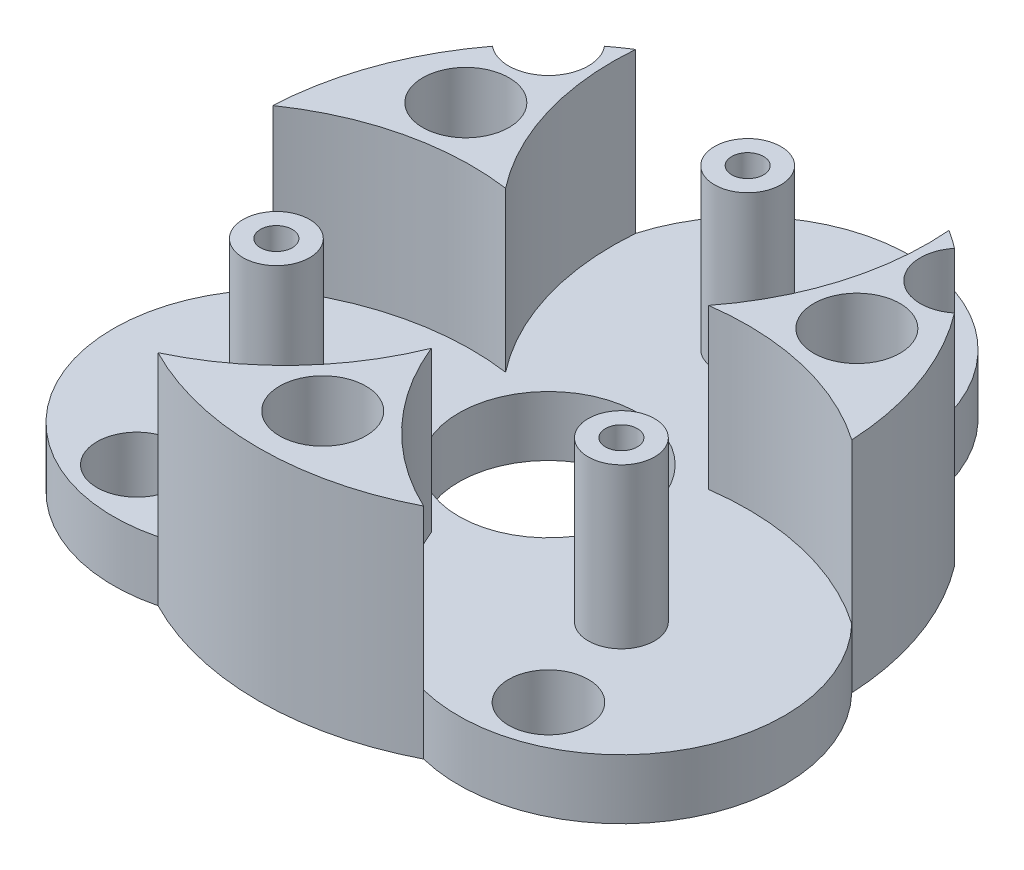
SolidWorks part; units mm, degrees
ref_plane "Alzado" through (0, 0, 0) normal (0, 0, 1) x (1, 0, 0)
ref_plane "Planta" through (0, 0, 0) normal (0, 1, 0) x (1, 0, 0)
ref_plane "Vista lateral" through (0, 0, 0) normal (1, 0, 0) x (0, 0, -1)
sketch "Croquis1" plane through (0, 0, 0) normal (0, 1, 0) x (1, 0, 0)
  circle A0 centre (0, 0) radius 5 construction
  circle A1 centre (0, 15) radius 10 construction
  circle A2 centre (0, 0) radius 25 construction
  circle A7 centre (0, 0) radius 21.825
  point P24 (0, 0)
  dimension "D1" = 10
  dimension "D2" = 20
  dimension "D3" = 43.65
extrude "Saliente-Extruir1" add sketch "Croquis1" along normal blind 4.5
sketch "Croquis2" plane through (0, 4.5, 0) normal (0, 1, 0) x (1, 0, 0)
  circle A0 centre (0, 0) radius 15 construction
  circle A1 centre (0, 15) radius 2.5
  circle A2 centre (12.9904, -7.5) radius 2.5
  circle A3 centre (-12.9904, -7.5) radius 2.5
  point P12 (0, 0)
  dimension "D1" = 30
  dimension "D2" = 5
  dimension "D3" = 3
extrude "Saliente-Extruir2" add sketch "Croquis2" along normal blind 12
hole_wizard "Taladro de margen para M121" positions "Croquis3" profile "Croquis4" hole size "M12" standard "ISO" end condition through all
sketch "Croquis3" plane through (0, 4.5, 0) normal (0, 1, 0) x (1, 0, 0)
  point P0 (0, 0)
sketch "Croquis4" plane through (0, 4.5, 0) normal (1, 0, 0) x (0, 0, 1)
  line L0 (0, 0) -> (0, 4.5)
  line L1 (0, 4.5) -> (6.75, 4.5)
  line L2 (6.75, 4.5) -> (6.75, 0)
  line L5 (6.75, 0) -> (0, 0)
  line L11 (0, -6.35) -> (0, 107.95) construction
  dimension "Diámetro de taladro hasta el siguiente" = 13.5
  dimension "Profundidad de taladro hasta el siguiente" = 4.5
sketch "Croquis5" plane through (0, 4.5, 0) normal (0, 1, 0) x (1, 0, 0)
  line L0 (0, 0) -> (-18.901, 10.9125) construction
  line L1 (-12.9904, -7.5) -> (0, 15) construction
  circle A0 centre (-12.9904, -7.5) radius 8.25 construction
  circle A1 centre (0, 15) radius 8.25 construction
  arc A4 (-7.6427, 4.4125) -> (-11.8002, 18.3599) centre (8.1271, 16.7067) cw
  arc A5 (-7.6427, 4.4125) -> (-21.8002, 1.0394) centre (-10.4048, -15.3916) ccw
  arc A6 (-11.8002, 18.3599) -> (-21.8002, 1.0394) centre (0, 0) ccw
  circle A7 centre (0, 0) radius 21.825 construction
  dimension "D1" = 20
  dimension "D2" = 13
extrude "Saliente-Extruir3" add sketch "Croquis5" along normal up to surface (12 mm away) up to face at (-12.9904, 16.5, 10)
sketch "Croquis8" plane through (0, 16.5, 0) normal (0, 1, 0) x (1, 0, 0)
  line L0 (-7.6427, 4.4125) -> (-18.901, 10.9125) construction
  circle A1 centre (-14.7224, 8.5) radius 1.7
  circle A2 centre (0, 0) radius 15 construction
  arc A3 (-11.8002, 18.3599) -> (-21.8002, 1.0394) centre (0, 0) ccw construction
  circle A4 centre (0, 0) radius 17 construction
  dimension "D1" = 3.4
  dimension "D2" = 2
extrude "Cortar-Extruir1" cut sketch "Croquis8" against normal up to surface (16.5 mm away) up to face at (0, 0, 6.75)
pattern_circular "MatrizC1" count 3 every 120 about axis through (0, 0, 0) along (0, 1, 0) of "Saliente-Extruir3", "Cortar-Extruir1"
hole_wizard "Taladro de margen para M21" positions "Croquis9" profile "Croquis10" hole size "M2" standard "ISO" end condition through all
sketch "Croquis9" plane through (0, 16.5, 0) normal (0, 1, 0) x (1, 0, 0)
  point P0 (12.9904, -7.5)
  point P4 (-12.9904, -7.5)
  point P7 (0, 15)
sketch "Croquis10" plane through (12.9904, 16.5, 7.5) normal (1, 0, 0) x (0, 0, 1)
  line L0 (0, 0) -> (0, 16.5)
  line L1 (0, 16.5) -> (1.2, 16.5)
  line L2 (1.2, 16.5) -> (1.2, 0)
  line L5 (1.2, 0) -> (0, 0)
  line L11 (0, -6.35) -> (0, 107.95) construction
  dimension "Diámetro de taladro hasta el siguiente" = 2.4
  dimension "Profundidad de taladro hasta el siguiente" = 16.5
sketch "Croquis11" plane through (0, 0, 0) normal (0, -1, 0) x (1, 0, 0)
  arc A0 (-10, 19.3992) -> (-21.8002, -1.0394) centre (0, 0) ccw construction
  arc A1 (-10, 19.3992) -> (-21.8002, -1.0394) centre (0, 0) ccw
  arc A2 (-21.8002, -1.0394) -> (-10, 19.3992) centre (-12.9904, 7.5) cw
  circle A3 centre (-12.9904, 7.5) radius 1.2 construction
  circle A4 centre (-12.9904, 7.5) radius 1.2 construction
extrude "Saliente-Extruir5" add sketch "Croquis11" against normal up to surface (4.5 mm away) up to face at (0, 4.5, 6.75)
pattern_circular "MatrizC2" count 3 every 120 about axis through (0, 0, 0) along (0, 1, 0) of "Saliente-Extruir5"
sketch "Croquis12" plane through (0, 0, 0) normal (0, -1, 0) x (1, 0, 0)
  circle A0 centre (-12.9904, 7.5) radius 2.875
  circle A1 centre (12.9904, 7.5) radius 2.875
  circle A2 centre (0, -15) radius 2.875
  point P10 (0, 0)
  dimension "D1" = 5.75
  dimension "D2" = 3
extrude "Cortar-Extruir2" cut sketch "Croquis12" against normal blind 2.2
sketch "Croquis13" plane through (0, 0, 0) normal (0, -1, 0) x (1, 0, 0)
  line L1 (15.5, -15.5) -> (-15.5, -15.5) construction
  line L2 (15.5, -15.5) -> (15.5, 15.5) construction
  line L3 (15.5, 15.5) -> (-15.5, 15.5) construction
  line L4 (-15.5, -15.5) -> (-15.5, 15.5) construction
  line L5 (15.5, -15.5) -> (-15.5, 15.5) construction
  line L6 (15.5, 15.5) -> (-15.5, -15.5) construction
  circle A0 centre (15.5, -15.5) radius 3
  circle A1 centre (-15.5, -15.5) radius 3
  circle A2 centre (-15.5, 15.5) radius 3
  circle A3 centre (15.5, 15.5) radius 3
  point P0 (0, 0)
  point P16 (0, 0)
  dimension "D2" = 6
  dimension "D1" = 31
  dimension "D3" = 4
extrude "Cortar-Extruir3" cut sketch "Croquis13" against normal up to surface (16.5 mm away) up to face at (-14.7224, 16.5, -6.8)
hole_wizard "Refrentado para tornillo con cabeza plana de M31" positions "Croquis14" profile "Croquis15" counterbore size "M3" standard "ISO" end condition through all
sketch "Croquis14" plane through (0, 16.5, 0) normal (0, 1, 0) x (1, 0, 0)
  point P0 (-14.7224, 8.5)
  point P3 (0, -17)
  point P6 (14.7224, 8.5)
sketch "Croquis15" plane through (-14.7224, 16.5, -8.5) normal (1, 0, 0) x (0, 0, 1)
  line L0 (0, 0) -> (0, 16.5)
  line L1 (0, 16.5) -> (1.7, 16.5)
  line L3 (1.7, 16.5) -> (1.7, 10)
  line L4 (1.7, 10) -> (3.25, 10)
  line L5 (3.25, 10) -> (3.25, 0)
  line L7 (3.25, 0) -> (0, 0)
  line L11 (0, -6.35) -> (0, 107.95) construction
  dimension "Diámetro de taladro hasta el siguiente" = 3.4
  dimension "Profundidad de taladro hasta el siguiente" = 16.5
  dimension "Diámetro de refrentado" = 6.5
  dimension "Profundidad de refrentado" = 10
